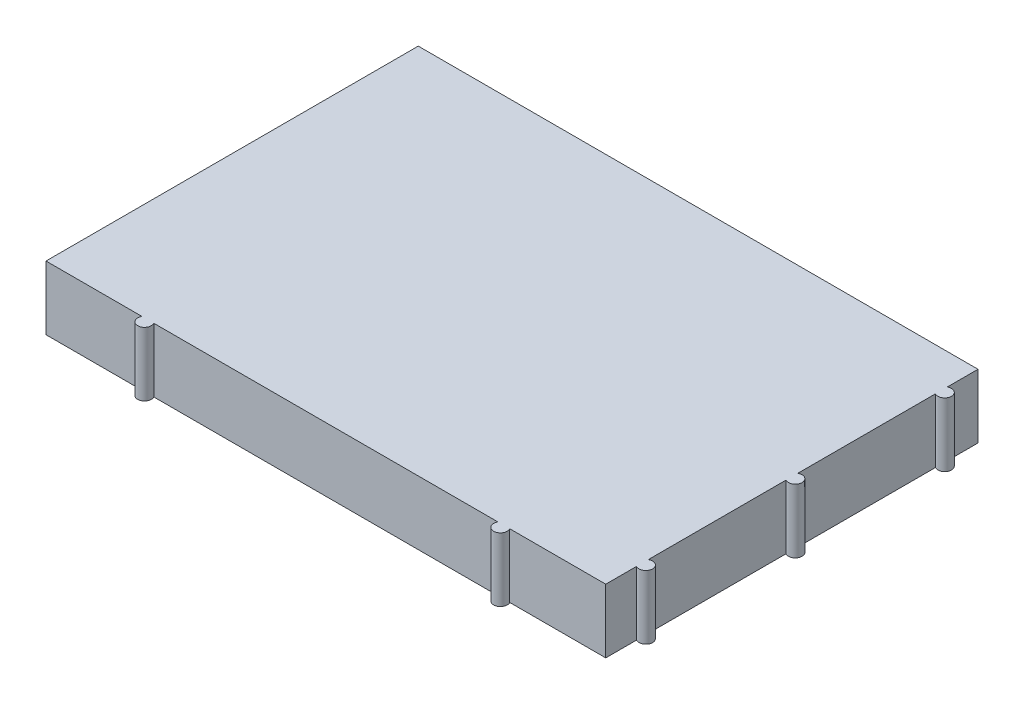
SolidWorks part; units mm, degrees
ref_plane "Front Plane" through (0, 0, 0) normal (0, 0, 1) x (1, 0, 0)
ref_plane "Top Plane" through (0, 0, 0) normal (0, 1, 0) x (1, 0, 0)
ref_plane "Right Plane" through (0, 0, 0) normal (1, 0, 0) x (0, 0, -1)
sketch "Sketch1" plane through (0, 0, 0) normal (0, 1, 0) x (1, 0, 0)
  line L0 (-27.066, -27.4) -> (-25.334, -27.4) construction
  line L1 (-41.2, -27.4) -> (-27.066, -27.4)
  line L2 (-41.2, -27.4) -> (-41.2, 27.4)
  line L3 (-41.2, 27.4) -> (41.2, 27.4)
  line L4 (41.2, -27.4) -> (41.2, -22.866)
  line L5 (-41.2, -27.4) -> (41.2, 27.4) construction
  line L6 (-41.2, 27.4) -> (41.2, -27.4) construction
  line L7 (-25.334, -27.4) -> (25.334, -27.4)
  line L8 (25.334, -27.4) -> (27.066, -27.4) construction
  line L9 (27.066, -27.4) -> (41.2, -27.4)
  line L10 (-41.2, 0) -> (41.2, 0) construction
  line L11 (41.2, 21.134) -> (41.2, 22.866) construction
  line L12 (41.2, 22.866) -> (41.2, 27.4)
  line L13 (41.2, 0) -> (41.2, 0.866) construction
  line L14 (41.2, 0.866) -> (41.2, 21.134)
  line L15 (41.2, -0.866) -> (41.2, 0) construction
  line L16 (41.2, -22.866) -> (41.2, -21.134) construction
  line L17 (41.2, -21.134) -> (41.2, -0.866)
  arc A0 (-27.066, -27.4) -> (-25.334, -27.4) centre (-26.2, -27.9) ccw
  arc A1 (25.334, -27.4) -> (27.066, -27.4) centre (26.2, -27.9) ccw
  arc A2 (41.2, -22.866) -> (41.2, -21.134) centre (41.7, -22) ccw
  arc A3 (41.2, -0.866) -> (41.2, 0.866) centre (41.7, 0) ccw
  arc A4 (41.2, 21.134) -> (41.2, 22.866) centre (41.7, 22) ccw
  arc A5 (-25.334, -27.4) -> (-27.066, -27.4) centre (-26.2, -27.9) ccw construction
  arc A6 (27.066, -27.4) -> (25.334, -27.4) centre (26.2, -27.9) ccw construction
  arc A7 (41.2, 22.866) -> (41.2, 21.134) centre (41.7, 22) ccw construction
  arc A8 (41.2, 0.866) -> (40.7, 0) centre (41.7, 0) ccw construction
  arc A9 (40.7, 0) -> (41.2, -0.866) centre (41.7, 0) ccw construction
  arc A10 (41.2, -21.134) -> (41.2, -22.866) centre (41.7, -22) ccw construction
  point P0 (0, 0)
  dimension "D3" = 2
  dimension "D1" = 82.4
  dimension "D2" = 54.8
  dimension "D4" = 0.5
  dimension "D5" = 0.5
  dimension "D6" = 15
  dimension "D7" = 15
  dimension "D8" = 22
  dimension "D9" = 22
extrude "Boss-Extrude1" add sketch "Sketch1" along normal blind 9.4
